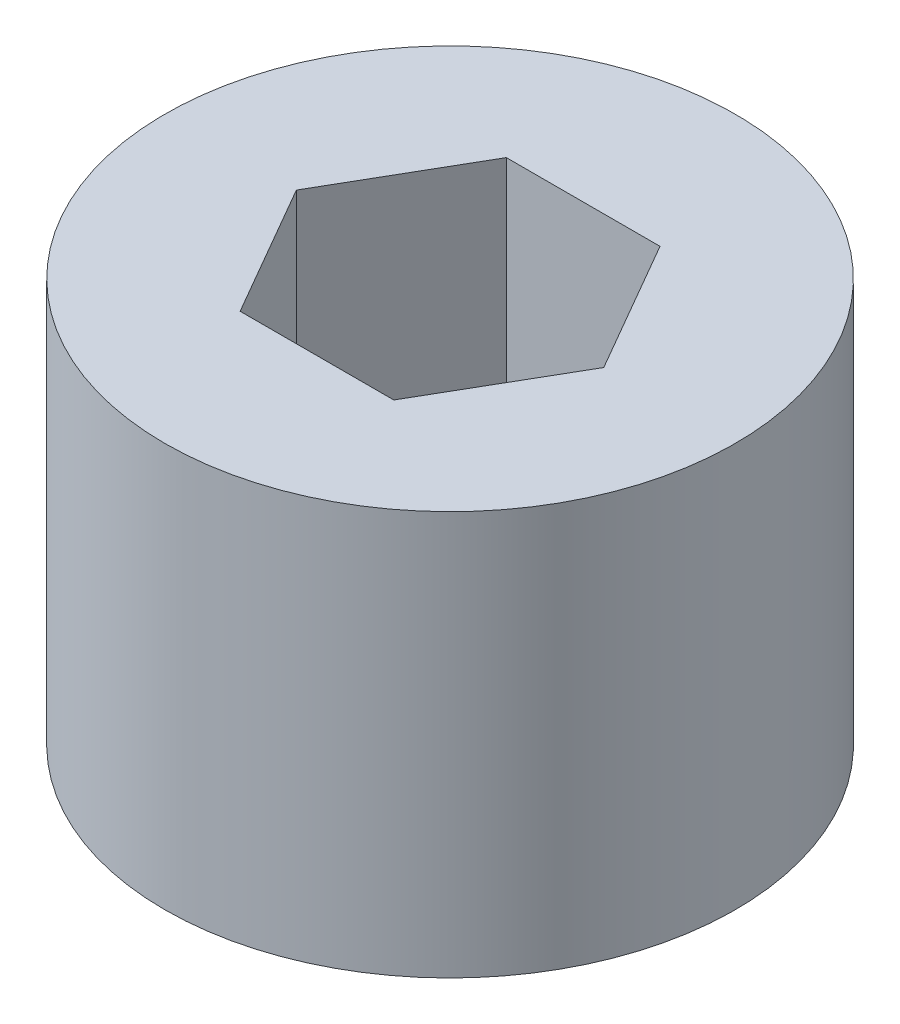
SolidWorks part; units mm, degrees
ref_plane "Front Plane" through (0, 0, 0) normal (0, 0, 1) x (1, 0, 0)
ref_plane "Top Plane" through (0, 0, 0) normal (0, 1, 0) x (1, 0, 0)
ref_plane "Right Plane" through (0, 0, 0) normal (1, 0, 0) x (0, 0, -1)
sketch "Sketch1" plane through (0, 0, 0) normal (0, 1, 0) x (1, 0, 0)
  circle A0 centre (0, 0) radius 15
  dimension "D1" = 30
extrude "Boss-Extrude1" add sketch "Sketch1" along normal blind 21.24
sketch "Sketch3" plane through (0, 21.24, 0) normal (0, 1, 0) x (1, 0, 0)
  line L1 (8.0829, 0) -> (4.0415, 7)
  line L2 (4.0415, 7) -> (-4.0415, 7)
  line L3 (-4.0415, 7) -> (-8.0829, 0)
  line L4 (-8.0829, 0) -> (-4.0415, -7)
  line L5 (-4.0415, -7) -> (4.0415, -7)
  line L6 (4.0415, -7) -> (8.0829, 0)
  circle A0 centre (0, 0) radius 7 construction
  dimension "D1" = 14
extrude "Cut-Extrude1" cut sketch "Sketch3" against normal blind 32 and the other way blind 26
equation "\"21.24.00mm\"=10"
